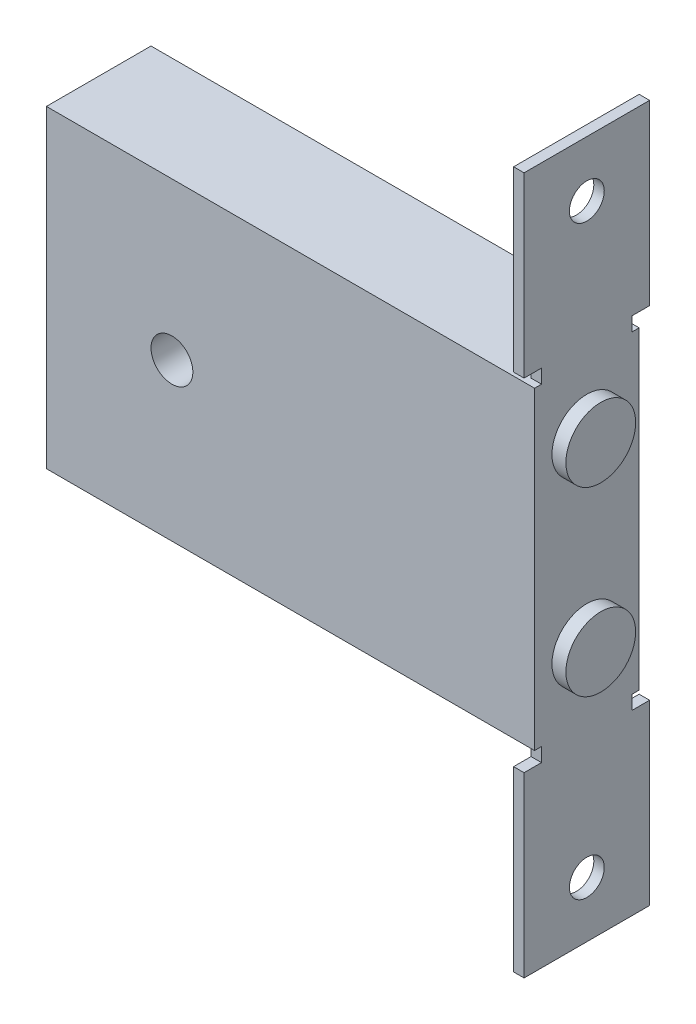
SolidWorks part; units mm, degrees
ref_plane "Front Plane" through (0, 0, 0) normal (0, 0, 1) x (1, 0, 0)
ref_plane "Top Plane" through (0, 0, 0) normal (0, 1, 0) x (1, 0, 0)
ref_plane "Right Plane" through (0, 0, 0) normal (1, 0, 0) x (0, 0, -1)
sketch "Sketch1" plane through (0, 0, 0) normal (0, 0, 1) x (1, 0, 0)
  line L1 (0, 0) -> (70, 0)
  line L2 (0, 0) -> (0, 45)
  line L3 (0, 45) -> (70, 45)
  line L4 (70, 0) -> (70, 45)
  circle A0 centre (18, 22.5) radius 3
  point P8 (0, 22.5)
  dimension "D3" = 6
  dimension "D4" = 18
  dimension "D1" = 70
  dimension "D2" = 45
extrude "Boss-Extrude1" add sketch "Sketch1" along normal blind 15
sketch "Sketch2" plane through (70, 0, 0) normal (1, 0, 0) x (0, 0, -1)
  line L0 (-1, 42.9534) -> (-1, 47)
  line L1 (-1, 47) -> (1.5, 47)
  line L2 (1.5, 47) -> (1.5, 72.5)
  line L3 (1.5, 72.5) -> (-16.5, 72.5)
  line L4 (0, 0) -> (0, 45) construction
  line L5 (-15, 45) -> (0, 45) construction
  line L6 (-1, 42.9534) -> (-14, 42.9534)
  line L7 (0, 22.5) -> (-7.5, 22.5) construction
  line L8 (-7.5, 22.5) -> (-7.5, 45) construction
  line L9 (-16.5, 47) -> (-16.5, 72.5)
  line L10 (-14, 47) -> (-16.5, 47)
  line L11 (-14, 42.9534) -> (-14, 47)
  line L12 (-14, 2.0466) -> (-14, -2)
  line L13 (-14, -2) -> (-16.5, -2)
  line L14 (-16.5, -2) -> (-16.5, -27.5)
  line L15 (-1, 2.0466) -> (-14, 2.0466)
  line L16 (1.5, -27.5) -> (-16.5, -27.5)
  line L17 (1.5, -2) -> (1.5, -27.5)
  line L18 (-1, -2) -> (1.5, -2)
  line L19 (-1, 2.0466) -> (-1, -2)
  circle A0 centre (-7.5, 64.5) radius 2.5
  circle A1 centre (-7.5, -19.5) radius 2.5
  point P9 (-7.5, 45)
  point P10 (0, 22.5)
  point P16 (-7.5, 42.9534)
  point P17 (-7.5, 72.5)
  point P19 (-7.5, -27.5)
  point P20 (-7.5, 2.0466)
  dimension "D5" = 5
  dimension "D6" = 8
  dimension "D1" = 1
  dimension "D2" = 9
  dimension "D3" = 2
  dimension "D4" = 50
extrude "Boss-Extrude2" add sketch "Sketch2" against normal blind 1.5
sketch "Sketch3" plane through (70, 0, 0) normal (1, 0, 0) x (0, 0, -1)
  line L0 (0, 22.5) -> (-15, 22.5) construction
  line L1 (0, 0) -> (0, 45) construction
  line L2 (-15, 0) -> (-15, 45) construction
  circle A0 centre (-7.5, 35.5) radius 5
  circle A2 centre (-7.5, 9.5) radius 5
  point P9 (-7.5, 22.5)
  dimension "D1" = 10
  dimension "D2" = 13
extrude "Boss-Extrude3" add sketch "Sketch3" along normal blind 2
